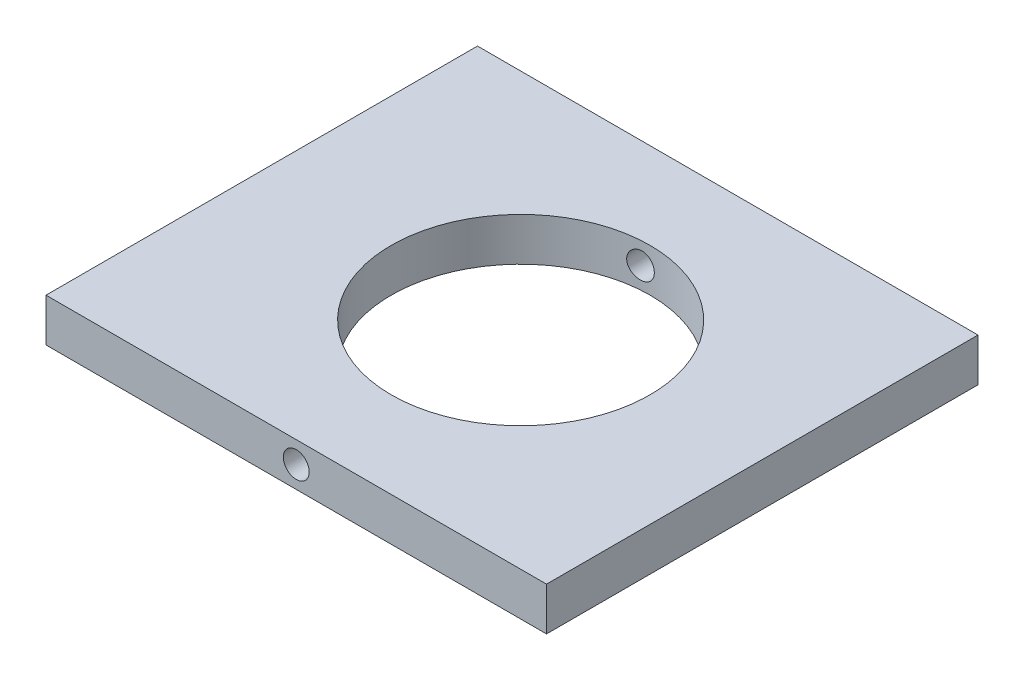
SolidWorks part; units mm, degrees
ref_plane "Plan de face" through (0, 0, 0) normal (0, 0, 1) x (1, 0, 0)
ref_plane "Plan de dessus" through (0, 0, 0) normal (0, 1, 0) x (1, 0, 0)
ref_plane "Plan de droite" through (0, 0, 0) normal (1, 0, 0) x (0, 0, -1)
sketch "Esquisse1" plane through (0, 0, 0) normal (0, 0, 1) x (1, 0, 0)
  line L0 (-5.5, -47.5) -> (52.5, -47.5) construction
  line L5 (-5.5, -45) -> (52.5, -45)
  line L6 (-5.5, -45) -> (-5.5, -50)
  line L7 (-5.5, -50) -> (52.5, -50)
  line L8 (52.5, -45) -> (52.5, -50)
  line L9 (23.5, -45) -> (23.5, -50) construction
  dimension "D1" = 5
  dimension "D2" = 58
extrude "Boss.-Extru.1" add sketch "Esquisse1" along normal blind 50
sketch "Esquisse2" plane through (0, -45, 0) normal (0, 1, 0) x (-1, 0, 0)
  line L0 (5.5, 50) -> (-52.5, 50) construction
  line L7 (-52.5, 50) -> (-52.5, 0) construction
  circle A0 centre (-24.5, 25) radius 15
  dimension "D10" = 28
  dimension "D11" = 25
extrude "Enlèv. mat.-Extru.1" cut sketch "Esquisse2" against normal through all
sketch "Esquisse5" plane through (0, 0, 50) normal (0, 0, 1) x (1, 0, 0)
  line L0 (-5.5, -45) -> (-5.5, -50) construction
  line L1 (-5.5, -50) -> (52.5, -50) construction
  circle A0 centre (23.5, -47.5) radius 1.5
  dimension "D1" = 29
  dimension "D2" = 2.5
extrude "Enlèv. mat.-Extru.4" cut sketch "Esquisse5" against normal through all
